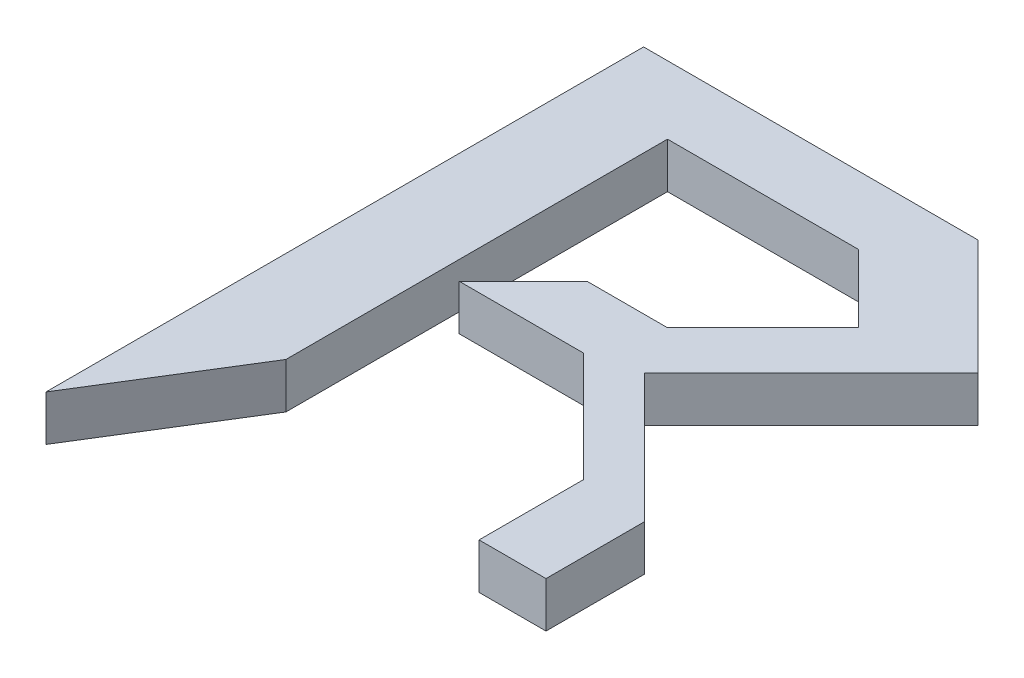
SolidWorks part; units mm, degrees
ref_plane "Front Plane" through (0, 0, 0) normal (0, 0, 1) x (1, 0, 0)
ref_plane "Top Plane" through (0, 0, 0) normal (0, 1, 0) x (1, 0, 0)
ref_plane "Right Plane" through (0, 0, 0) normal (1, 0, 0) x (0, 0, -1)
sketch "Sketch1" plane through (0, 0, 0) normal (0, 1, 0) x (1, 0, 0)
  line L0 (-339.7994, 126.3047) -> (-339.7994, 191.9929)
  line L1 (-339.7994, 191.9929) -> (-303.0401, 191.9929)
  line L2 (-303.0401, 191.9929) -> (-290.4006, 179.3534)
  line L3 (-290.4006, 179.3534) -> (-308.7345, 161.0195)
  line L4 (-308.7345, 161.0195) -> (-294.5528, 146.8377)
  line L5 (-294.5528, 146.8377) -> (-294.5528, 136.019)
  line L6 (-294.5528, 136.019) -> (-301.911, 136.019)
  line L7 (-301.911, 136.019) -> (-301.911, 147.5004)
  line L8 (-301.911, 147.5004) -> (-313.9598, 159.5492)
  line L9 (-313.9598, 159.5492) -> (-327.6187, 159.5492)
  line L10 (-327.6187, 159.5492) -> (-320.592, 166.576)
  line L11 (-320.592, 166.576) -> (-311.7537, 166.576)
  line L12 (-311.7537, 166.576) -> (-301.2686, 177.0611)
  line L13 (-301.2686, 177.0611) -> (-308.7345, 184.527)
  line L14 (-308.7345, 184.527) -> (-329.7048, 184.527)
  line L15 (-329.7048, 184.527) -> (-329.7048, 142.5863)
  line L16 (-329.7048, 142.5863) -> (-339.7994, 126.3047)
  point P2 (-289.7126, 178.6654)
  point P18 (-306.2316, 162.9329)
  point P19 (-178.5614, 15.686)
  point P20 (0, 0)
  point P21 (-304.3336, 142.5863)
  point P22 (-307.2915, 162.4625)
  point P23 (-301.911, 147.5004)
  point P24 (-294.8622, 147.5004)
extrude "Boss-Extrude1" add sketch "Sketch1" along normal blind 5 contours L15 L16 L0 L1 L2 L3 L4 L5 L6 L7 L8 L9 L10 L11 L12 L13 L14
